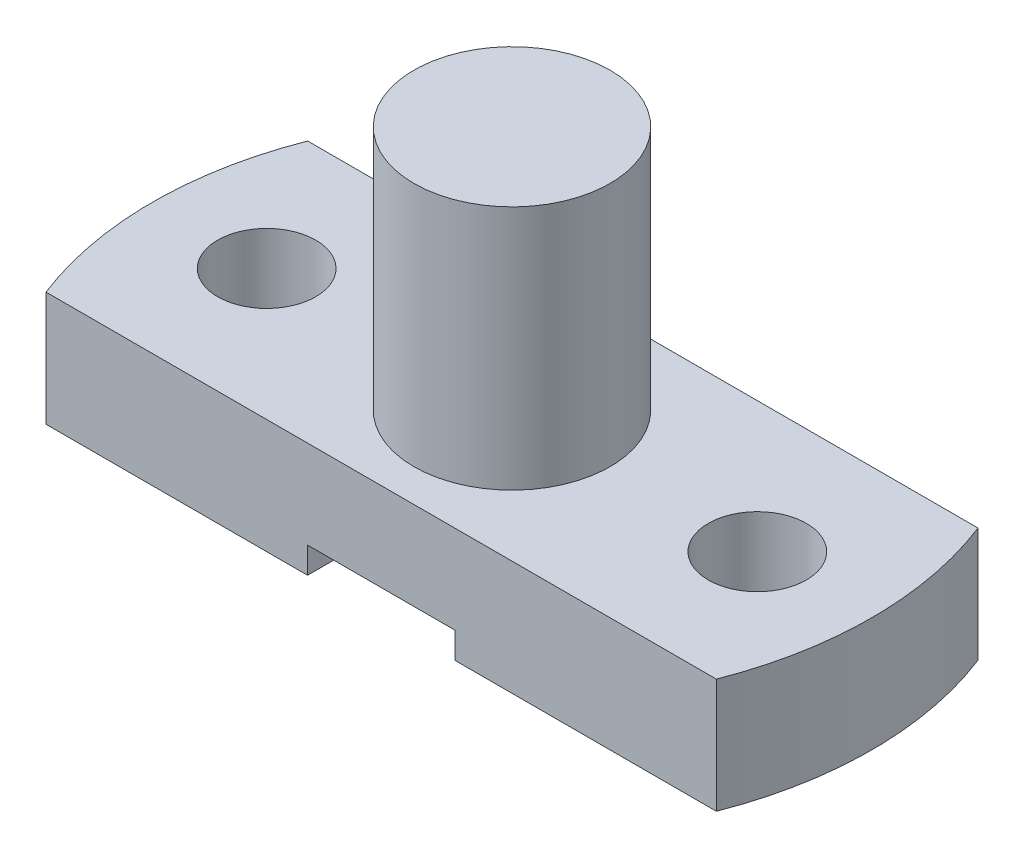
SolidWorks part; units mm, degrees
ref_plane "Front Plane" through (0, 0, 0) normal (0, 0, 1) x (1, 0, 0)
ref_plane "Top Plane" through (0, 0, 0) normal (0, 1, 0) x (1, 0, 0)
ref_plane "Right Plane" through (0, 0, 0) normal (1, 0, 0) x (0, 0, -1)
sketch "Sketch1" plane through (0, 0, 0) normal (0, 1, 0) x (1, 0, 0)
  line L0 (0, 0) -> (0, 48.924) construction
  line L1 (0, 0) -> (50.5021, 0) construction
  line L2 (-102.4695, 40) -> (102.4695, 40)
  line L3 (-102.4695, -40) -> (102.4695, -40)
  circle A1 centre (75, 0) radius 15
  circle A2 centre (-75, 0) radius 15
  arc A3 (-102.4695, 40) -> (-102.4695, -40) centre (0, 0) ccw
  arc A4 (102.4695, -40) -> (102.4695, 40) centre (0, 0) ccw
  dimension "D2" = 30
  dimension "D4" = 220
  dimension "D3" = 75
  dimension "D5" = 40
  dimension "D6" = 40
extrude "Boss-Extrude2" add sketch "Sketch1" along normal blind 35
sketch "Sketch2" plane through (0, 35, 0) normal (0, 1, 0) x (1, 0, 0)
  circle A0 centre (0, 0) radius 30
  dimension "D1" = 60
extrude "Boss-Extrude3" add sketch "Sketch2" along normal blind 75
sketch "Sketch3" plane through (0, 0, 0) normal (0, -1, 0) x (1, 0, 0)
  line L0 (0, 0) -> (0, 31.0588) construction
  line L1 (22.5, 40) -> (22.5, -40)
  line L2 (-102.4695, 40) -> (102.4695, 40) construction
  line L3 (102.4695, -40) -> (-102.4695, -40) construction
  line L4 (-22.5, 40) -> (-22.5, -40)
  line L5 (-22.5, 40) -> (22.5, 40)
  line L6 (22.5, -40) -> (-22.5, -40)
  dimension "D1" = 45
extrude "Cut-Extrude1" cut sketch "Sketch3" against normal blind 8
